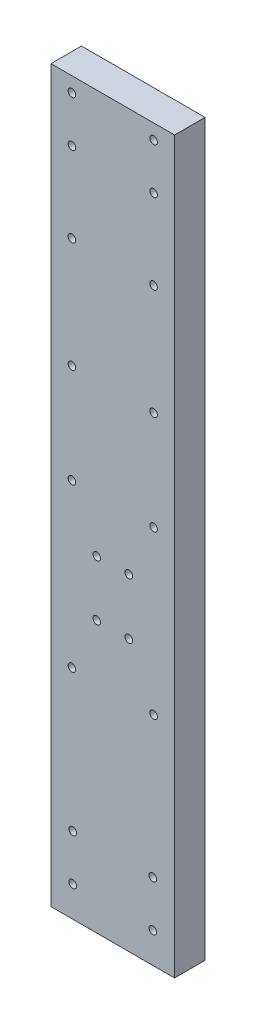
SolidWorks part; units mm, degrees
ref_plane "Front Plane" through (0, 0, 0) normal (0, 0, 1) x (1, 0, 0)
ref_plane "Top Plane" through (0, 0, 0) normal (0, 1, 0) x (1, 0, 0)
ref_plane "Right Plane" through (0, 0, 0) normal (1, 0, 0) x (0, 0, -1)
sketch "Sketch3" plane through (0, 0, 0) normal (0, 0, 1) x (1, 0, 0)
  line L0 (0, 95.5064) -> (0, -0.1536)
  line L1 (16.2, 95.5064) -> (16.2, -0.1536)
  line L2 (0, -0.1536) -> (16.2, -0.1536)
  line L4 (0, 95.5064) -> (16.2, 95.5064)
  line L5 (0, 13.8464) -> (16.2, 13.8464) construction
  line L6 (0, 60.1064) -> (16.2, 60.1064) construction
  line L26 (0, 52.1064) -> (16.2, 52.1064) construction
  line L27 (0, 25.8464) -> (16.2, 25.8464) construction
  line L30 (0, 79.5614) -> (16.2, 79.5614) construction
  line L32 (0, 85.5614) -> (16.2, 85.5614) construction
  circle A0 centre (6, 35.3464) radius 0.5
  circle A1 centre (10.2, 35.3464) radius 0.5
  circle A2 centre (2.75, 87.5614) radius 0.5
  circle A3 centre (10.2, 42.6664) radius 0.5
  circle A4 centre (13.45, 49.6064) radius 0.5
  circle A5 centre (2.75, 93.5614) radius 0.5
  circle A6 centre (13.45, 87.5614) radius 0.5
  circle A7 centre (2.75, 62.6064) radius 0.5
  circle A16 centre (2.85, 9.8464) radius 0.5
  circle A17 centre (13.35, 9.8464) radius 0.5
  circle A18 centre (13.35, 3.8464) radius 0.5
  circle A19 centre (2.85, 3.8464) radius 0.5
  circle A20 centre (13.45, 62.6064) radius 0.5
  circle A21 centre (2.75, 77.0614) radius 0.5
  circle A22 centre (13.45, 28.3464) radius 0.5
  circle A23 centre (13.45, 77.0614) radius 0.5
  circle A24 centre (13.45, 93.5614) radius 0.5
  circle A25 centre (2.75, 28.3464) radius 0.5
  circle A26 centre (6, 42.6064) radius 0.5
  circle A27 centre (2.75, 49.6064) radius 0.5
  dimension "D1" = 2.5
  dimension "D2" = 9.5
  dimension "D32" = 6
  dimension "D33" = 6
  dimension "D3" = 2.5
  dimension "D4" = 9.5
  dimension "D5" = 6
  dimension "D6" = 2.75
  dimension "D7" = 2.75
  dimension "D8" = 6
  dimension "D9" = 2.5
  dimension "D10" = 2.5
  dimension "D11" = 9.5
  dimension "D12" = 9.44
  dimension "D13" = 2.75
  dimension "D14" = 6
  dimension "D15" = 2.75
  dimension "D16" = 6
  dimension "D17" = 12
  dimension "D18" = 4
  dimension "D19" = 4
  dimension "D20" = 6
  dimension "D21" = 6
  dimension "D22" = 4
  dimension "D23" = 2.85
  dimension "D24" = 2.85
  dimension "D25" = 26.26
  dimension "D26" = 16.2
  dimension "D27" = 8
  dimension "D28" = 2.5
  dimension "D29" = 2.5
  dimension "D30" = 2.75
  dimension "D31" = 2.75
  dimension "D34" = 2.5
  dimension "D35" = 2.5
  dimension "D36" = 2.75
  dimension "D37" = 2.75
  dimension "D38" = 19.455
  dimension "D39" = 6
  dimension "D40" = 2
  dimension "D41" = 2
  dimension "D42" = 2.75
  dimension "D43" = 2.75
  dimension "D44" = 4
  dimension "D46" = 2.75
  dimension "D47" = 2.75
  dimension "D48" = 9.945
extrude "Boss-Extrude3" add sketch "Sketch3" along normal blind 4
equation "\"D25@Sketch3\"= \"HL@parametersSketch@prostheticParameters.SLDPRT\" * 0.196 - 4 - 6'Index PIP length"
equation "\"D26@Sketch3\"= \"fingerWidth@parametersSketch@prostheticParameters.SLDPRT\"'Index Width"
equation "\"D38@Sketch3\"= \"HL@parametersSketch@prostheticParameters.SLDPRT\" * 0.143 - 3 - 4 'Index MIP Length"
equation "\"D48@Sketch3\"= \"HL@parametersSketch@prostheticParameters.SLDPRT\" * 0.097 - 3 - 5'Index DIP Length - Gap Fingertip"
